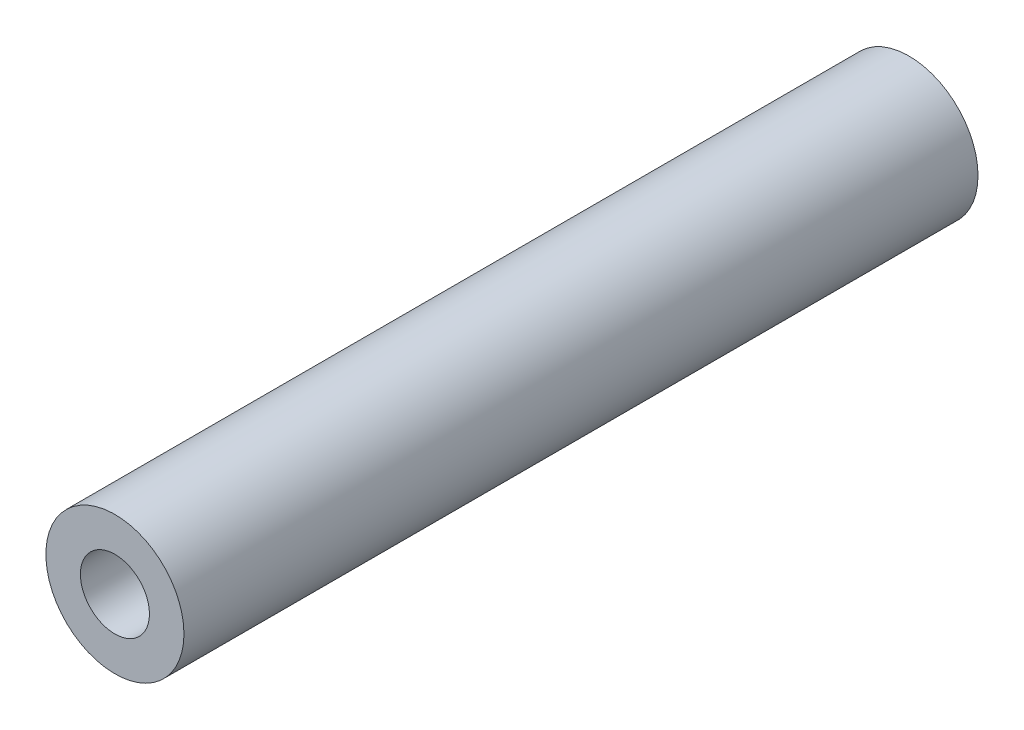
SolidWorks part; units mm, degrees
ref_plane "Plan de face" through (0, 0, 0) normal (0, 0, 1) x (1, 0, 0)
ref_plane "Plan de dessus" through (0, 0, 0) normal (0, 1, 0) x (1, 0, 0)
ref_plane "Plan de droite" through (0, 0, 0) normal (1, 0, 0) x (0, 0, -1)
sketch "Esquisse1" plane through (0, 0, 0) normal (0, 0, 1) x (1, 0, 0)
  circle A0 centre (0, 0) radius 4
extrude "Extrusion2" add sketch "Esquisse1" along normal blind 46
sketch "Esquisse2" plane through (0, 0, 46) normal (0, 0, 1) x (1, 0, 0)
  circle A0 centre (0, 0) radius 2
extrude "Extrusion3" cut sketch "Esquisse2" against normal blind 10
sketch "Esquisse3" plane through (0, 0, 0) normal (0, 0, -1) x (-1, 0, 0)
  circle A0 centre (0, 0) radius 2
extrude "Extrusion4" cut sketch "Esquisse3" against normal blind 10
